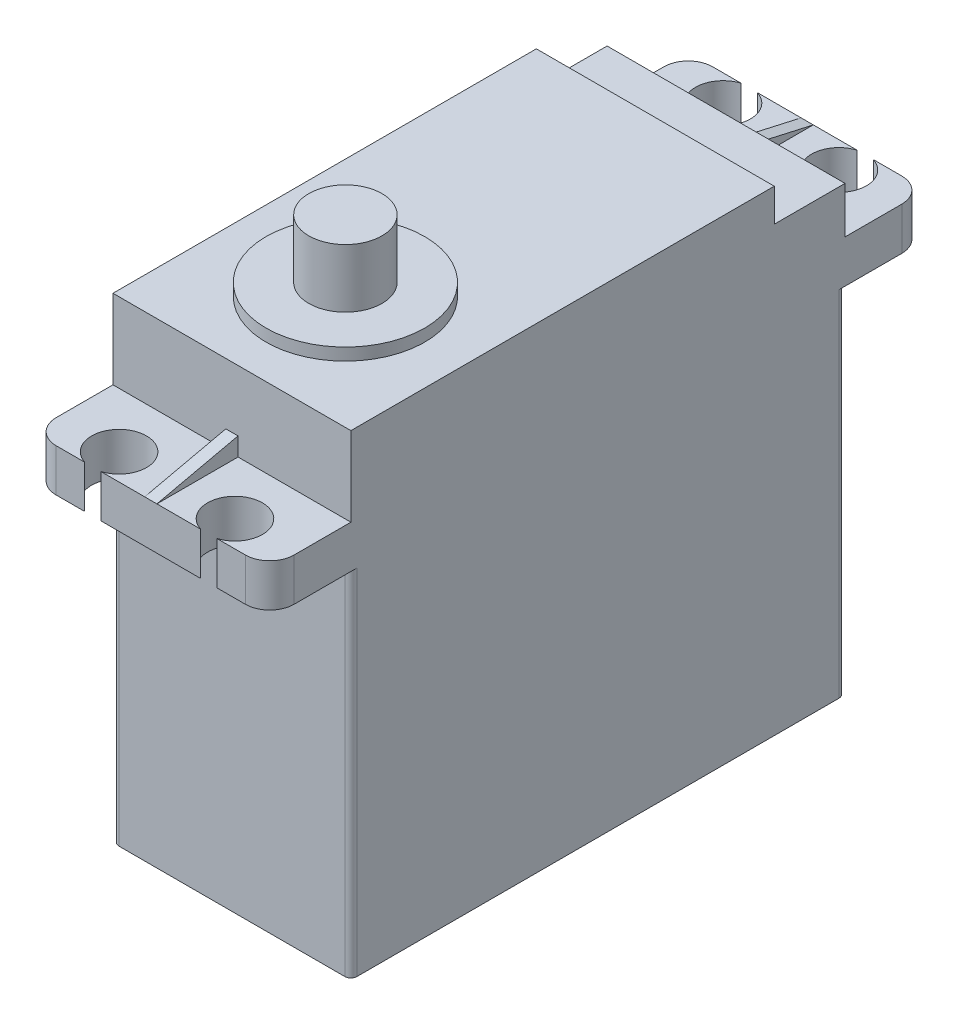
SolidWorks part; units mm, degrees
ref_plane "Front Plane" through (0, 0, 0) normal (0, 0, 1) x (1, 0, 0)
ref_plane "Top Plane" through (0, 0, 0) normal (0, 1, 0) x (1, 0, 0)
ref_plane "Right Plane" through (0, 0, 0) normal (1, 0, 0) x (0, 0, -1)
sketch "Sketch1" plane through (0, 0, 0) normal (1, 0, 0) x (0, 0, -1)
  line L0 (-40.5, 0) -> (0, 0)
  line L1 (0, 0) -> (0, 29)
  line L2 (0, 32.5) -> (6.65, 32.5)
  line L3 (6.65, 32.5) -> (6.65, 29)
  line L4 (6.65, 29) -> (0, 29)
  line L5 (0, 32.5) -> (0, 36.3)
  line L6 (0, 36.3) -> (-5.8, 36.3)
  line L7 (-5.8, 36.3) -> (-5.8, 39)
  line L8 (-5.8, 39) -> (-40.5, 39)
  line L9 (-40.5, 39) -> (-40.5, 32.5)
  line L10 (-40.5, 32.5) -> (-47.15, 32.5)
  line L11 (-47.15, 32.5) -> (-47.15, 29)
  line L12 (-47.15, 29) -> (-40.5, 29)
  line L13 (-40.5, 29) -> (-40.5, 0)
  dimension "D1" = 40.5
  dimension "D2" = 29
  dimension "D3" = 53.8
  dimension "D4" = 36.3
  dimension "D5" = 5.8
  dimension "D6" = 39
  dimension "D9" = 3.5
extrude "Main" add sketch "Sketch1" along normal mid plane 19.5
sketch "Sketch4" plane through (0, 39, 0) normal (0, 1, 0) x (1, 0, 0)
  line L0 (9.75, -40.5) -> (-9.75, -40.5) construction
  line L1 (9.75, -40.5) -> (-9.75, -40.5) construction
  circle A0 centre (0, -31.2) radius 6.5
  point P4 (0, -40.5)
  dimension "D2" = 13
  dimension "D1" = 9.3
extrude "BaseCircle" add sketch "Sketch4" along normal blind 1
sketch "Sketch5" plane through (0, 40, 0) normal (0, 1, 0) x (1, 0, 0)
  circle A1 centre (0, -31.2) radius 3
  dimension "D1" = 6
extrude "Gear" add sketch "Sketch5" along normal blind 4.8
sketch "Sketch9" plane through (0, 32.5, 0) normal (0, 1, 0) x (-1, 0, 0)
  line L0 (-9.75, 40.5) -> (9.75, 40.5) construction
  line L1 (-9.75, 0) -> (9.75, 0) construction
  line L2 (-9.75, -6.65) -> (-9.75, 0) construction
  line L3 (9.75, -6.65) -> (9.75, 0) construction
  circle A0 centre (-4.75, 45) radius 2.25
  circle A1 centre (4.75, 45) radius 2.25
  circle A2 centre (4.75, -4.5) radius 2.25
  circle A3 centre (-4.75, -4.5) radius 2.25
  dimension "D6" = 4.5
  dimension "D9" = 5
  dimension "D1" = 4.5
  dimension "D7" = 4.5
  dimension "D10" = 5
  dimension "D11" = 9.5
extrude "Fixing-Hole" cut sketch "Sketch9" against normal blind 19.05
fillet "FixingFillet" radius 2 4 edges at (9.75, 30.75, -6.65) (-9.75, 30.75, -6.65) (-9.75, 30.75, 47.15) (9.75, 30.75, 47.15)
sketch "Esquisse1" plane through (0, 0, 0) normal (1, 0, 0) x (0, 0, -1)
  line L0 (6.65, 32.5) -> (0, 34)
  line L1 (0, 34) -> (0, 32.5)
  line L2 (0, 32.5) -> (6.65, 32.5)
  line L3 (-47.15, 32.5) -> (-40.5, 32.5)
  line L4 (-40.5, 32.5) -> (-40.5, 34)
  line L5 (-40.5, 39) -> (-40.5, 32.5) construction
  line L6 (-40.5, 34) -> (-47.15, 32.5)
  dimension "D1" = 1.5
extrude "Reinforcement" add sketch "Esquisse1" along normal mid plane 1
fillet "ServoFillet" radius 0.5 4 edges at (9.75, 14.5, 40.5) (-9.75, 14.5, 40.5) (9.75, 14.5, 0) (-9.75, 14.5, 0)
